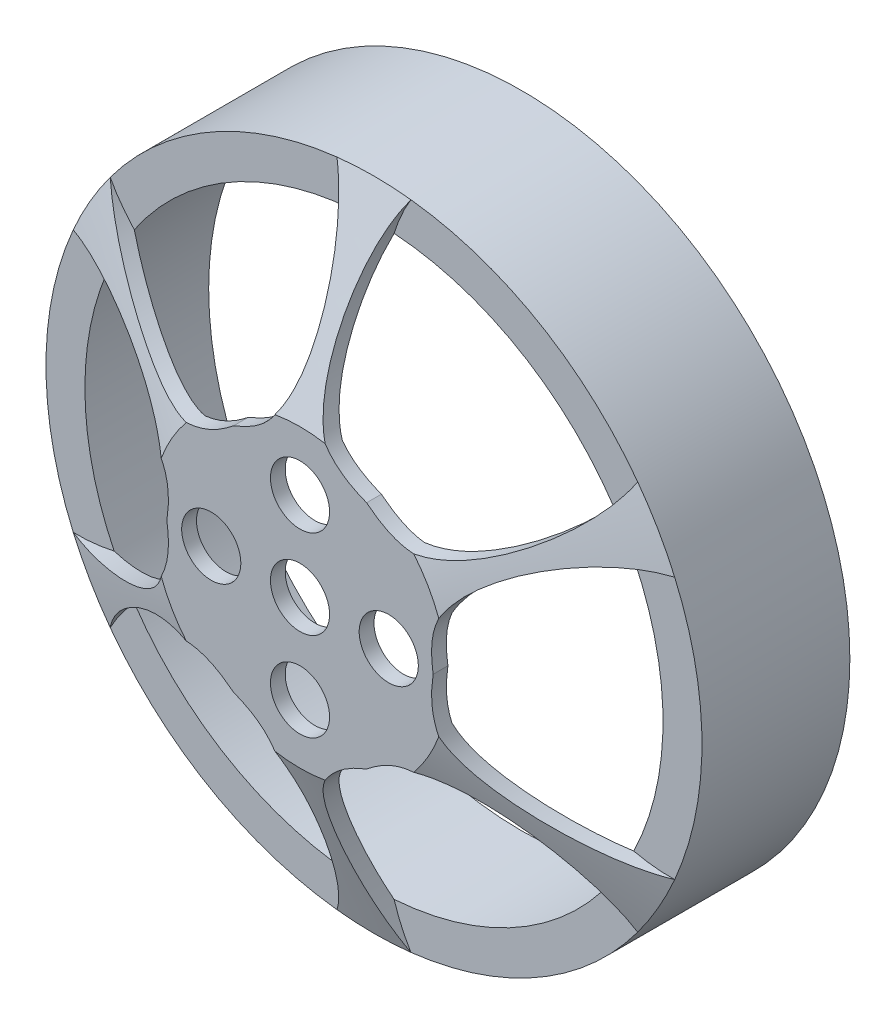
SolidWorks part; units mm, degrees
ref_plane "Front Plane" through (0, 0, 0) normal (0, 0, 1) x (1, 0, 0)
ref_plane "Top Plane" through (0, 0, 0) normal (0, 1, 0) x (1, 0, 0)
ref_plane "Right Plane" through (0, 0, 0) normal (1, 0, 0) x (0, 0, -1)
sketch "Sketch1" plane through (0, 0, 0) normal (0, 0, 1) x (1, 0, 0)
  circle A0 centre (0, 0) radius 22.175
  dimension "D1" = 44.35
extrude "Boss-Extrude1" add sketch "Sketch1" along normal blind 10
ref_plane "Plane1" through (0, 0, 15) normal (0, 0, 1) x (1, 0, 0)
sketch "Sketch2" plane through (0, 0, 15) normal (0, 0, 1) x (1, 0, 0)
  circle A0 centre (0, 0) radius 10
  dimension "D1" = 20
loft "Loft1" add profiles "Sketch2" section "Sketch2" section edge at (22.175, 0, 10)
shell "Shell1" thickness 1
sketch "Sketch3" plane through (0, 0, 15) normal (0, 0, 1) x (1, 0, 0)
  line L0 (0, 0) -> (0, 26.9567) construction
  line L1 (0, 0) -> (23.3452, 13.4783) construction
  line L2 (0, 0) -> (23.3452, -13.4783) construction
  line L3 (0, 0) -> (0, -26.9567) construction
  line L4 (0, 0) -> (-23.3452, -13.4783) construction
  line L5 (0, 0) -> (-23.3452, 13.4783) construction
  line L6 (-2.5, 22.0336) -> (0, 18.0894) construction
  line L7 (0, 18.0894) -> (0, 11.1143) construction
  line L8 (0, 0) -> (-13.4569, 23.308) construction
  line L9 (0, 11.1143) -> (-1.0311, 9.1637) construction
  line L10 (-1.0311, 9.1637) -> (-4.5, 7.7942) construction
  line L11 (-17.8317, 13.1819) -> (-15.6659, 9.0447) construction
  line L12 (-15.6659, 9.0447) -> (-9.6253, 5.5571) construction
  line L13 (-9.6253, 5.5571) -> (-7.4205, 5.4748) construction
  line L14 (-7.4205, 5.4748) -> (-4.5, 7.7942) construction
  line L15 (17.8317, 13.1819) -> (15.6659, 9.0447) construction
  line L16 (15.6659, 9.0447) -> (9.6253, 5.5571) construction
  line L17 (9.6253, 5.5571) -> (7.4205, 5.4748) construction
  line L18 (7.4205, 5.4748) -> (4.5, 7.7942) construction
  line L19 (2.5, 22.0336) -> (0, 18.0894) construction
  line L20 (0, 18.0894) -> (0, 11.1143) construction
  line L21 (0, 11.1143) -> (1.0311, 9.1637) construction
  line L22 (1.0311, 9.1637) -> (4.5, 7.7942) construction
  line L23 (20.3317, -8.8517) -> (15.6659, -9.0447) construction
  line L24 (15.6659, -9.0447) -> (9.6253, -5.5571) construction
  line L25 (9.6253, -5.5571) -> (8.4516, -3.6889) construction
  line L26 (8.4516, -3.6889) -> (9, 0) construction
  line L27 (20.3317, 8.8517) -> (15.6659, 9.0447) construction
  line L28 (15.6659, 9.0447) -> (9.6253, 5.5571) construction
  line L29 (9.6253, 5.5571) -> (8.4516, 3.6889) construction
  line L30 (8.4516, 3.6889) -> (9, 0) construction
  line L31 (2.5, -22.0336) -> (0, -18.0894) construction
  line L32 (0, -18.0894) -> (0, -11.1143) construction
  line L33 (0, -11.1143) -> (1.0311, -9.1637) construction
  line L34 (1.0311, -9.1637) -> (4.5, -7.7942) construction
  line L35 (17.8317, -13.1819) -> (15.6659, -9.0447) construction
  line L36 (15.6659, -9.0447) -> (9.6253, -5.5571) construction
  line L37 (9.6253, -5.5571) -> (7.4205, -5.4748) construction
  line L38 (7.4205, -5.4748) -> (4.5, -7.7942) construction
  line L39 (-17.8317, -13.1819) -> (-15.6659, -9.0447) construction
  line L40 (-15.6659, -9.0447) -> (-9.6253, -5.5571) construction
  line L41 (-9.6253, -5.5571) -> (-7.4205, -5.4748) construction
  line L42 (-7.4205, -5.4748) -> (-4.5, -7.7942) construction
  line L43 (-2.5, -22.0336) -> (0, -18.0894) construction
  line L44 (0, -18.0894) -> (0, -11.1143) construction
  line L45 (0, -11.1143) -> (-1.0311, -9.1637) construction
  line L46 (-1.0311, -9.1637) -> (-4.5, -7.7942) construction
  line L47 (-20.3317, 8.8517) -> (-15.6659, 9.0447) construction
  line L48 (-15.6659, 9.0447) -> (-9.6253, 5.5571) construction
  line L49 (-9.6253, 5.5571) -> (-8.4516, 3.6889) construction
  line L50 (-8.4516, 3.6889) -> (-9, 0) construction
  line L51 (-20.3317, -8.8517) -> (-15.6659, -9.0447) construction
  line L52 (-15.6659, -9.0447) -> (-9.6253, -5.5571) construction
  line L53 (-9.6253, -5.5571) -> (-8.4516, -3.6889) construction
  line L54 (-8.4516, -3.6889) -> (-9, 0) construction
  circle A0 centre (0, 0) radius 2
  circle A1 centre (0, 0) radius 6 construction
  circle A6 centre (0, 0) radius 9 construction
  arc A7 (-20.3317, 8.8517) -> (-20.3317, -8.8517) centre (0, 0) ccw
  circle A8 centre (0, 6) radius 2
  circle A9 centre (0, 0) radius 22.175 construction
  circle A10 centre (6, 0) radius 2
  circle A11 centre (0, -6) radius 2
  circle A12 centre (-6, 0) radius 2
  arc A13 (-2.5, 22.0336) -> (-17.8317, 13.1819) centre (0, 0) ccw
  arc A14 (17.8317, 13.1819) -> (2.5, 22.0336) centre (0, 0) ccw
  arc A15 (20.3317, -8.8517) -> (20.3317, 8.8517) centre (0, 0) ccw
  arc A16 (-17.8317, -13.1819) -> (-2.5, -22.0336) centre (0, 0) ccw
  arc A17 (2.5, -22.0336) -> (17.8317, -13.1819) centre (0, 0) ccw
  spline S0 degree 4 poles (-2.5, 22.0336) (0, 18.0894) (0, 11.1143) (-1.0311, 9.1637) (-4.5, 7.7942) knots 0 0 0 0 0 1 1 1 1 1
  spline S1 degree 4 poles (-17.8317, 13.1819) (-15.6659, 9.0447) (-9.6253, 5.5571) (-7.4205, 5.4748) (-4.5, 7.7942) knots 0 0 0 0 0 1 1 1 1 1
  spline S2 degree 4 poles (17.8317, 13.1819) (15.6659, 9.0447) (9.6253, 5.5571) (7.4205, 5.4748) (4.5, 7.7942) knots 0 0 0 0 0 1 1 1 1 1
  spline S3 degree 4 poles (2.5, 22.0336) (0, 18.0894) (0, 11.1143) (1.0311, 9.1637) (4.5, 7.7942) knots 0 0 0 0 0 1 1 1 1 1
  spline S4 degree 4 poles (20.3317, -8.8517) (15.6659, -9.0447) (9.6253, -5.5571) (8.4516, -3.6889) (9, 0) knots 0 0 0 0 0 1 1 1 1 1
  spline S5 degree 4 poles (20.3317, 8.8517) (15.6659, 9.0447) (9.6253, 5.5571) (8.4516, 3.6889) (9, 0) knots 0 0 0 0 0 1 1 1 1 1
  spline S6 degree 4 poles (2.5, -22.0336) (0, -18.0894) (0, -11.1143) (1.0311, -9.1637) (4.5, -7.7942) knots 0 0 0 0 0 1 1 1 1 1
  spline S7 degree 4 poles (17.8317, -13.1819) (15.6659, -9.0447) (9.6253, -5.5571) (7.4205, -5.4748) (4.5, -7.7942) knots 0 0 0 0 0 1 1 1 1 1
  spline S8 degree 4 poles (-17.8317, -13.1819) (-15.6659, -9.0447) (-9.6253, -5.5571) (-7.4205, -5.4748) (-4.5, -7.7942) knots 0 0 0 0 0 1 1 1 1 1
  spline S9 degree 4 poles (-2.5, -22.0336) (0, -18.0894) (0, -11.1143) (-1.0311, -9.1637) (-4.5, -7.7942) knots 0 0 0 0 0 1 1 1 1 1
  spline S10 degree 4 poles (-20.3317, 8.8517) (-15.6659, 9.0447) (-9.6253, 5.5571) (-8.4516, 3.6889) (-9, 0) knots 0 0 0 0 0 1 1 1 1 1
  spline S11 degree 4 poles (-20.3317, -8.8517) (-15.6659, -9.0447) (-9.6253, -5.5571) (-8.4516, -3.6889) (-9, 0) knots 0 0 0 0 0 1 1 1 1 1
  point P15 (0, 0)
  point P21 (0, 0)
  point P81 (0, 0)
  point P83 (0, 0)
  dimension "D1" = 4
  dimension "D3" = 4
  dimension "D7" = 18
  dimension "D8" = 4
  dimension "D2" = 12
  dimension "D4" = 6
  dimension "D5" = 30
  dimension "D6" = 2.5
extrude "Cut-Extrude1" cut sketch "Sketch3" against normal blind 5
